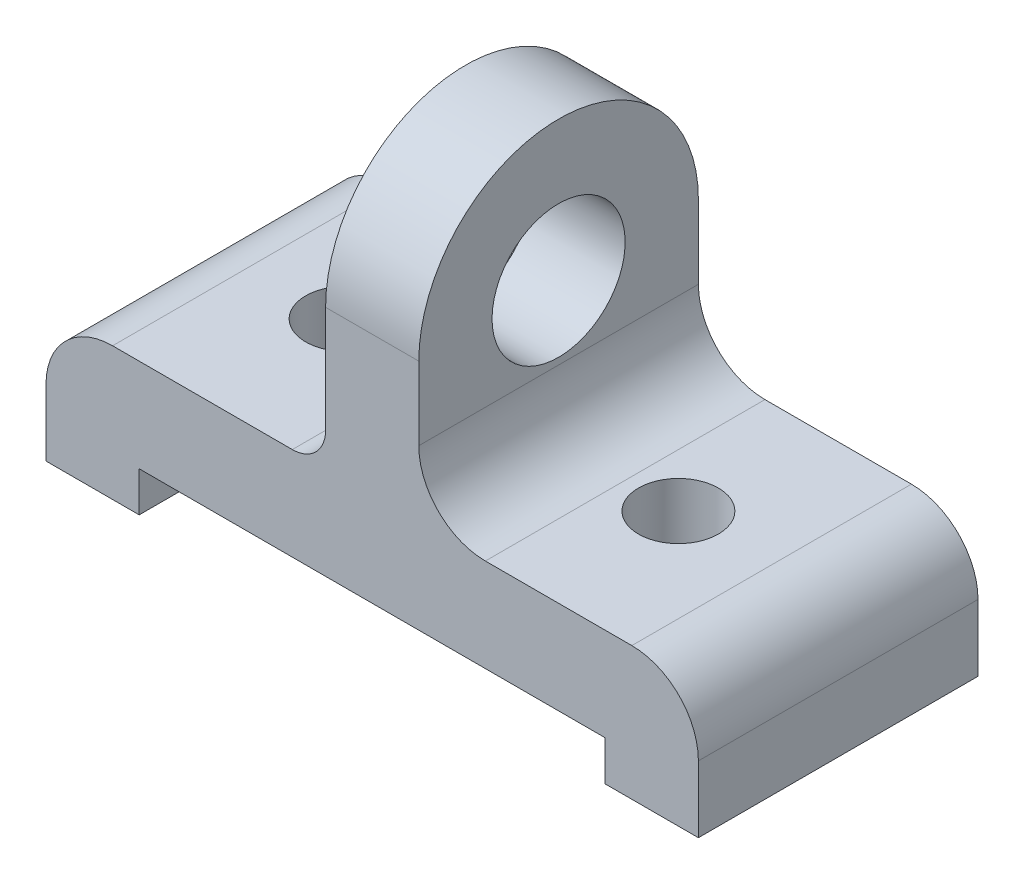
SolidWorks part; units mm, degrees
ref_plane "Front Plane" through (0, 0, 0) normal (0, 0, 1) x (1, 0, 0)
ref_plane "Top Plane" through (0, 0, 0) normal (0, 1, 0) x (1, 0, 0)
ref_plane "Right Plane" through (0, 0, 0) normal (1, 0, 0) x (0, 0, -1)
sketch "Sketch2" plane through (0, 0, 0) normal (0, 1, 0) x (1, 0, 0)
  line L0 (49, -21) -> (25, -21) construction
  line L1 (-49, 21) -> (49, 21)
  line L2 (-49, 21) -> (-49, -21)
  line L3 (-49, -21) -> (49, -21)
  line L4 (49, 21) -> (49, -21)
  line L5 (-49, 21) -> (49, -21) construction
  line L6 (-49, -21) -> (49, 21) construction
  line L7 (25, -21) -> (25, 0) construction
  line L8 (0, 21) -> (0, -21) construction
  circle A0 centre (25, 0) radius 6
  circle A1 centre (-25, 0) radius 6
  point P0 (0, 0)
  dimension "D4" = 12
  dimension "D1" = 42
  dimension "D2" = 98
  dimension "D3" = 24
extrude "Boss-Extrude1" add sketch "Sketch2" against normal blind 20
sketch "Sketch3" plane through (0, 0, 21) normal (0, 0, 1) x (1, 0, 0)
  line L0 (-49, -20) -> (-35, -20)
  line L1 (-49, -20) -> (49, -20) construction
  line L2 (-35, -20) -> (-35, -14)
  line L3 (-35, -14) -> (35, -14)
  line L4 (35, -14) -> (35, -20)
  line L5 (35, -20) -> (49, -20)
  line L6 (-35, -20) -> (35, -20)
  line M8 (-49, -20) -> (49, -20)
  dimension "D1" = 14
  dimension "D2" = 6
  dimension "D3" = 14
extrude "Cut-Extrude2" cut sketch "Sketch3" against normal blind 20 contours L4 L3 L2 M8
sketch "Sketch4" plane through (0, 0, -21) normal (0, 0, -1) x (-1, 0, 0)
  line L0 (-49, -20) -> (-35, -20)
  line L1 (-49, -20) -> (-49, 0) construction
  line L2 (-49, -20) -> (49, -20) construction
  line L3 (-35, -20) -> (-35, -14)
  line L4 (-35, -14) -> (35, -14)
  line L5 (35, -14) -> (35, -20)
  line L6 (35, -20) -> (49, -20)
  line L7 (-35, -20) -> (35, -20)
  line M3 (-49, -20) -> (49, -20)
extrude "Cut-Extrude3" cut sketch "Sketch4" against normal blind 20 contours L5 L4 L3 M3
sketch "Sketch5" plane through (0, 0, 1) normal (0, 0, 1) x (1, 0, 0)
  line L1 (30.9161, -14) -> (35, -14)
  line L2 (30.9161, -14) -> (30.9161, -20)
  line L3 (30.9161, -20) -> (35, -20)
  line L4 (35, -14) -> (35, -20)
extrude "Cut-Extrude4" cut sketch "Sketch5" against normal blind 20
sketch "Sketch6" plane through (0, 0, 1) normal (0, 0, 1) x (1, 0, 0)
  line L1 (-35, -14) -> (-30.9161, -14)
  line L2 (-35, -14) -> (-35, -20)
  line L3 (-35, -20) -> (-30.9161, -20)
  line L4 (-30.9161, -14) -> (-30.9161, -20)
extrude "Cut-Extrude5" cut sketch "Sketch6" against normal blind 20
sketch "Sketch7" plane through (0, 0, 1) normal (0, 0, 1) x (1, 0, 0)
  line L1 (-19.0839, -14) -> (19.0839, -14)
  line L2 (-19.0839, -14) -> (-19.0839, -20)
  line L3 (-19.0839, -20) -> (19.0839, -20)
  line L4 (19.0839, -14) -> (19.0839, -20)
extrude "Cut-Extrude6" cut sketch "Sketch7" against normal blind 20
ref_plane "Plane1" through (0, 0, 0) normal (-1, 0, 0) x (0, 0, 1)
sketch "Sketch8" plane through (0, 0, 0) normal (-1, 0, 0) x (0, 0, 1)
  line L1 (-21, 0) -> (21, 0)
  line L2 (-21, 0) -> (-21, 21)
  line L4 (21, 0) -> (21, 21)
  arc A0 (21, 21) -> (-21, 21) centre (0, 21) ccw
  circle A1 centre (0, 21) radius 10
  dimension "D1" = 21
  dimension "D2" = 42
extrude "Boss-Extrude2" add sketch "Sketch8" against normal mid plane 14
fillet "Fillet2" radius 5 1 edges at (-7, 0, 0)
fillet "Fillet3" radius 10 3 edges at (7, 0, 0) (49, 0, 0) (-49, 0, 0)
